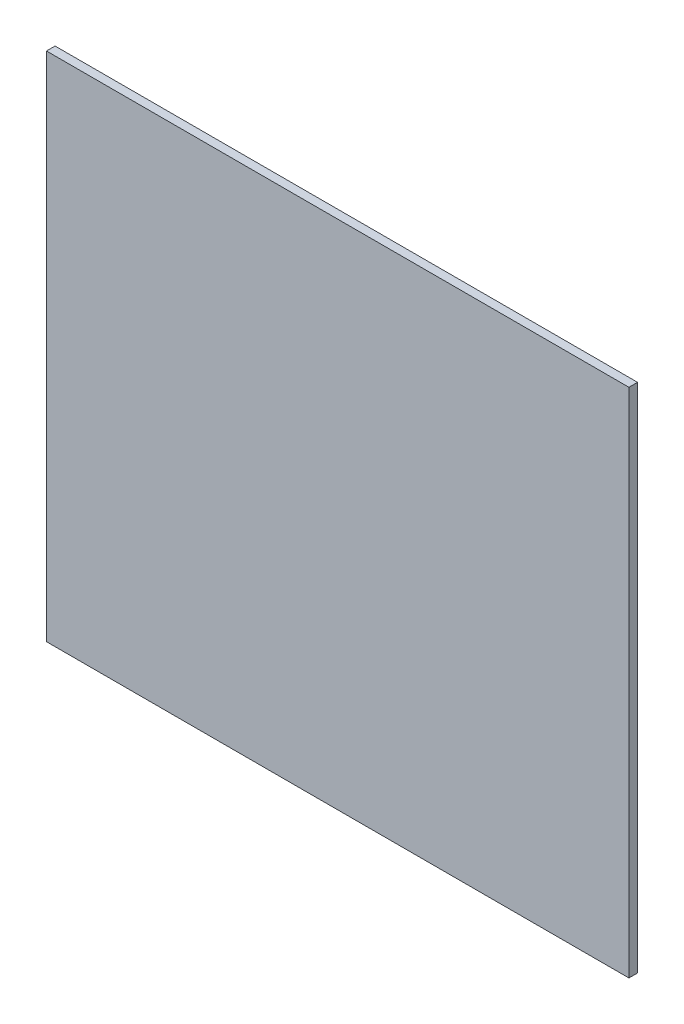
SolidWorks part; units mm, degrees
ref_plane "Front Plane" through (0, 0, 0) normal (0, 0, 1) x (1, 0, 0)
ref_plane "Top Plane" through (0, 0, 0) normal (0, 1, 0) x (1, 0, 0)
ref_plane "Right Plane" through (0, 0, 0) normal (1, 0, 0) x (0, 0, -1)
sketch "Sketch1" plane through (0, 0, 0) normal (0, 0, 1) x (1, 0, 0)
  line L1 (16.3638, 108.3854) -> (131.3638, 108.3854)
  line L2 (16.3638, 108.3854) -> (16.3638, 7.3854)
  line L3 (16.3638, 7.3854) -> (131.3638, 7.3854)
  line L4 (131.3638, 108.3854) -> (131.3638, 7.3854)
  dimension "D1" = 115
  dimension "D2" = 101
extrude "Boss-Extrude1" add sketch "Sketch1" along normal blind 1.7
